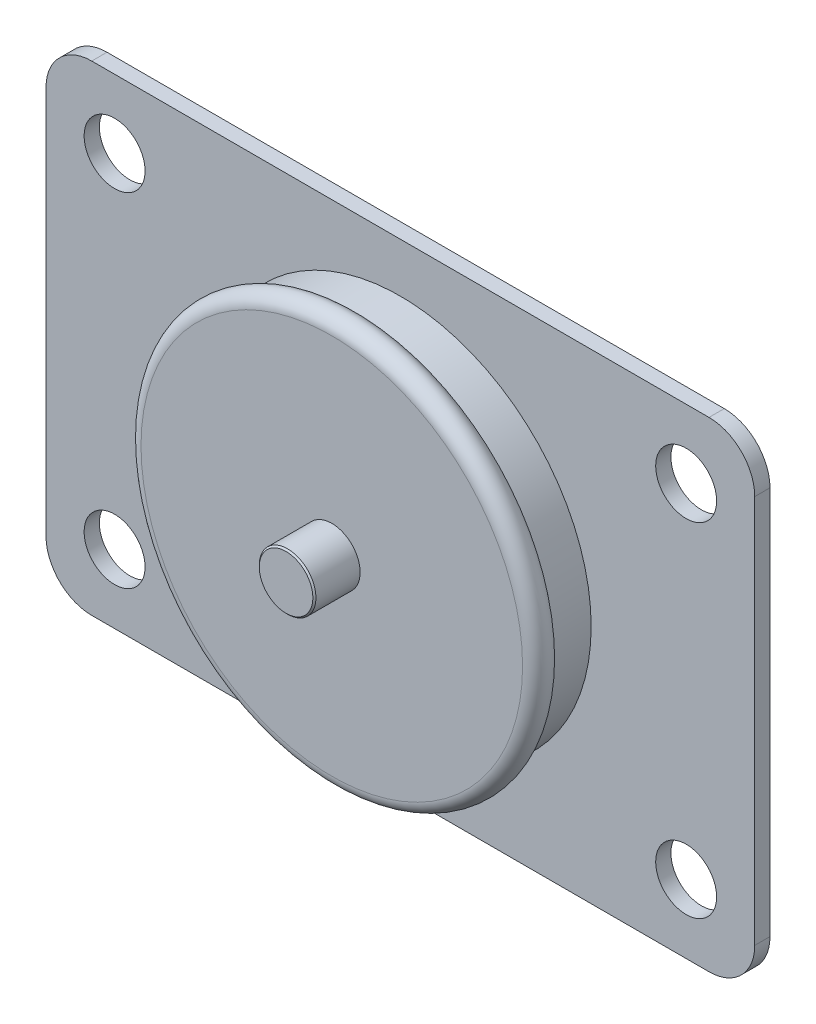
SolidWorks part; units mm, degrees
ref_plane "前视基准面" through (0, 0, 0) normal (0, 0, 1) x (1, 0, 0)
ref_plane "上视基准面" through (0, 0, 0) normal (0, 1, 0) x (1, 0, 0)
ref_plane "右视基准面" through (0, 0, 0) normal (1, 0, 0) x (0, 0, -1)
sketch "草图1" plane through (0, 0, 0) normal (0, 0, 1) x (1, 0, 0)
  line L0 (-40.3284, 19.6716) -> (-34.6716, 25.3284) construction
  line L1 (40.5, -31.5) -> (-40.5, -31.5)
  line L2 (46.5, -25.5) -> (46.5, 25.5)
  line L3 (40.5, 31.5) -> (-40.5, 31.5)
  line L4 (-46.5, -25.5) -> (-46.5, 25.5)
  line L5 (46.5, -31.5) -> (-46.5, 31.5) construction
  line L6 (46.5, 31.5) -> (-46.5, -31.5) construction
  line L11 (37.5, -22.5) -> (-37.5, 22.5) construction
  line L12 (37.5, 22.5) -> (-37.5, -22.5) construction
  line L13 (-43.1569, 22.5) -> (-37.5, 28.1569)
  line L14 (-37.5, 16.8431) -> (-31.8431, 22.5)
  line L15 (34.6716, 25.3284) -> (40.3284, 19.6716) construction
  line L16 (37.5, 28.1569) -> (43.1569, 22.5)
  line L17 (31.8431, 22.5) -> (37.5, 16.8431)
  line L18 (34.6716, -25.3284) -> (40.3284, -19.6716) construction
  line L19 (31.8431, -22.5) -> (37.5, -16.8431)
  line L20 (37.5, -28.1569) -> (43.1569, -22.5)
  line L21 (-34.6716, -25.3284) -> (-40.3284, -19.6716) construction
  line L22 (-37.5, -28.1569) -> (-43.1569, -22.5)
  line L23 (-31.8431, -22.5) -> (-37.5, -16.8431)
  arc A0 (-40.5, -31.5) -> (-46.5, -25.5) centre (-40.5, -25.5) cw
  arc A1 (40.5, -31.5) -> (46.5, -25.5) centre (40.5, -25.5) ccw
  arc A2 (46.5, 25.5) -> (40.5, 31.5) centre (40.5, 25.5) ccw
  arc A3 (-40.5, 31.5) -> (-46.5, 25.5) centre (-40.5, 25.5) ccw
  arc A4 (-43.1569, 22.5) -> (-37.5, 16.8431) centre (-40.3284, 19.6716) ccw
  arc A5 (-31.8431, 22.5) -> (-37.5, 28.1569) centre (-34.6716, 25.3284) ccw
  arc A6 (37.5, 28.1569) -> (31.8431, 22.5) centre (34.6716, 25.3284) ccw
  arc A7 (37.5, 16.8431) -> (43.1569, 22.5) centre (40.3284, 19.6716) ccw
  arc A8 (31.8431, -22.5) -> (37.5, -28.1569) centre (34.6716, -25.3284) ccw
  arc A9 (43.1569, -22.5) -> (37.5, -16.8431) centre (40.3284, -19.6716) ccw
  arc A10 (-37.5, -28.1569) -> (-31.8431, -22.5) centre (-34.6716, -25.3284) ccw
  arc A11 (-37.5, -16.8431) -> (-43.1569, -22.5) centre (-40.3284, -19.6716) ccw
  point P0 (0, 0)
  point P6 (0, 0)
  point P25 (-37.5, 22.5)
  point P31 (37.5, 22.5)
  point P38 (37.5, -22.5)
  point P45 (-37.5, -22.5)
  dimension "D5" = 6
  dimension "D1" = 93
  dimension "D2" = 63
  dimension "D3" = 75
  dimension "D4" = 45
extrude "凸台-拉伸1" add sketch "草图1" against normal blind 2
sketch "草图4" plane through (0, 0, 0) normal (0, 0, 1) x (1, 0, 0)
  circle A0 centre (0, 0) radius 25.0348
extrude "凸台-拉伸2" add sketch "草图4" along normal blind 9
sketch "草图5" plane through (0, 0, 0) normal (0, 1, 0) x (1, 0, 0)
  line L0 (-25.0348, 0) -> (-25.0348, -9) construction
  line L1 (0, 0) -> (0, -18.2551) construction
  circle A0 centre (-25.0348, -7.2601) radius 1.7399
revolve "旋转2" add sketch "草图5" angle 360 about L1
sketch "草图7" plane through (0, 0, 9) normal (0, 0, 1) x (1, 0, 0)
  circle A0 centre (0, 0) radius 3.717
extrude "凸台-拉伸3" add sketch "草图7" along normal blind 6
cosmetic thread "装饰螺纹线1" parameters "D2"=4.891
chamfer "倒角1" distance 0.2 angle 45 1 edges at (3.717, 0, 15)
sketch "草图9" plane through (0, 0, -2) normal (0, 0, -1) x (-1, 0, 0)
  circle A0 centre (0, 0) radius 25
extrude "切除-拉伸2" cut sketch "草图9" against normal blind 0.36
sketch "草图10" plane through (0, 0, -2) normal (0, 0, -1) x (-1, 0, 0)
sketch "草图12" plane through (0, 0, -2) normal (0, 0, -1) x (-1, 0, 0)
  line L0 (-40.3284, 19.6716) -> (-34.6716, 25.3284) construction
  line L5 (37.5, -22.5) -> (-37.5, 22.5) construction
  line L6 (37.5, 22.5) -> (-37.5, -22.5) construction
  line L9 (34.6716, 25.3284) -> (40.3284, 19.6716) construction
  line L10 (37.5, 28.1569) -> (43.1569, 22.5)
  line L11 (31.8431, 22.5) -> (37.5, 16.8431)
  line L12 (40.3284, -19.6716) -> (34.6716, -25.3284) construction
  line L13 (43.1569, -22.5) -> (37.5, -28.1569)
  line L14 (37.5, -16.8431) -> (31.8431, -22.5)
  line L15 (-34.6716, -25.3284) -> (-40.3284, -19.6716) construction
  line L16 (-37.5, -28.1569) -> (-43.1569, -22.5)
  line L17 (-31.8431, -22.5) -> (-37.5, -16.8431)
  line L18 (-43.1569, 22.5) -> (-37.5, 28.1569)
  line L19 (-37.5, 16.8431) -> (-31.8431, 22.5)
  arc A3 (37.5, 28.1569) -> (31.8431, 22.5) centre (34.6716, 25.3284) ccw
  arc A4 (37.5, 16.8431) -> (43.1569, 22.5) centre (40.3284, 19.6716) ccw
  arc A5 (43.1569, -22.5) -> (37.5, -16.8431) centre (40.3284, -19.6716) ccw
  arc A6 (31.8431, -22.5) -> (37.5, -28.1569) centre (34.6716, -25.3284) ccw
  arc A7 (-43.1569, 22.5) -> (-37.5, 16.8431) centre (-40.3284, 19.6716) ccw
  arc A8 (-31.8431, 22.5) -> (-37.5, 28.1569) centre (-34.6716, 25.3284) ccw
  arc A9 (-37.5, -28.1569) -> (-31.8431, -22.5) centre (-34.6716, -25.3284) ccw
  arc A10 (-37.5, -16.8431) -> (-43.1569, -22.5) centre (-40.3284, -19.6716) ccw
  point P0 (0, 0)
  point P8 (-37.5, 22.5)
  point P17 (37.5, 22.5)
  point P24 (37.5, -22.5)
  point P31 (-37.5, -22.5)
  dimension "D1" = 75
  dimension "D2" = 45
extrude "凸台-拉伸4" add sketch "草图12" against normal blind 2
sketch "草图13" plane through (0, 0, -2) normal (0, 0, -1) x (-1, 0, 0)
  line L5 (37.5, -22.5) -> (-37.5, 22.5) construction
  line L6 (37.5, 22.5) -> (-37.5, -22.5) construction
  circle A0 centre (-37.5, 22.5) radius 4
  circle A1 centre (-37.5, -22.5) radius 4
  circle A2 centre (37.5, -22.5) radius 4
  circle A3 centre (37.5, 22.5) radius 4
  point P0 (0, 0)
  dimension "D1" = 75
  dimension "D2" = 45
extrude "切除-拉伸3" cut sketch "草图13" against normal blind 35
